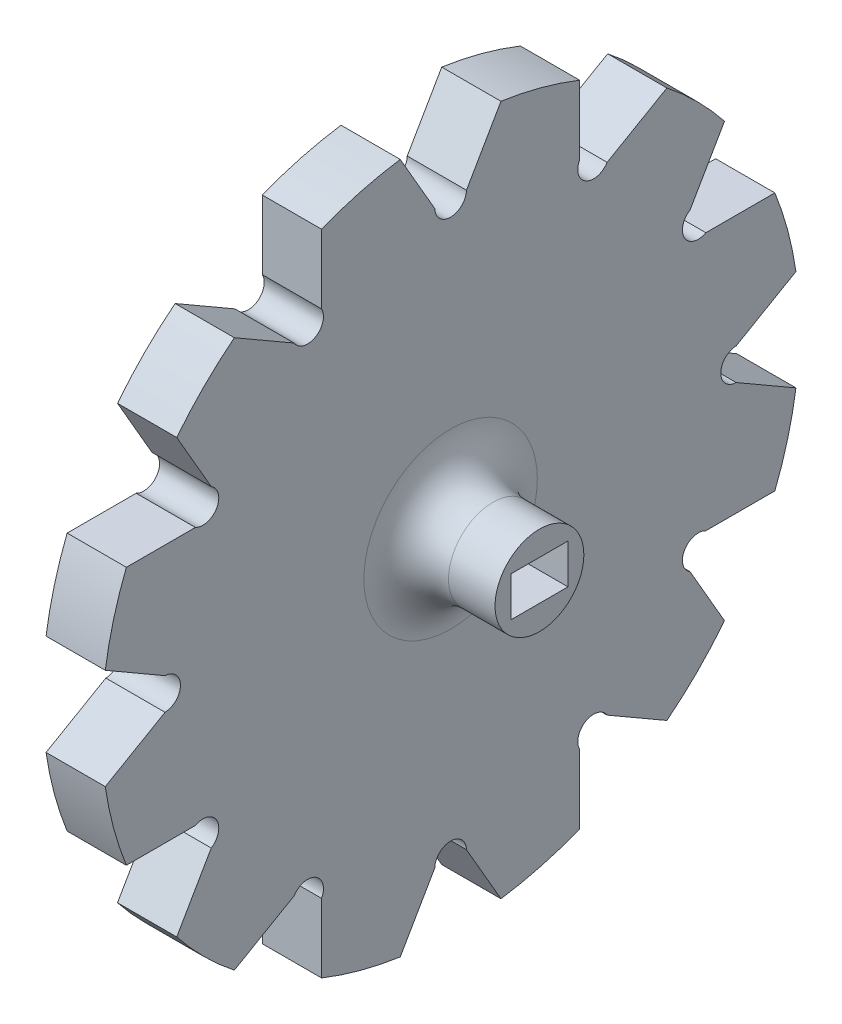
SolidWorks part; units mm, degrees
ref_plane "Front" through (0, 0, 0) normal (0, 0, 1) x (1, 0, 0)
ref_plane "Top" through (0, 0, 0) normal (0, 1, 0) x (1, 0, 0)
ref_plane "Right" through (0, 0, 0) normal (1, 0, 0) x (0, 0, -1)
sketch "Sketch3" plane through (0, 0, 0) normal (1, 0, 0) x (0, 0, -1)
  line L0 (0, -27.0459) -> (0, 27.0459) construction
  line L1 (0, 0) -> (7, 26.1244) construction
  line L2 (0, 0) -> (-7, 26.1244) construction
  circle A0 centre (0, 0) radius 27.0459
  dimension "D1" = 15
  dimension "D2" = 14
extrude "Boss-Extrude1" add sketch "Sketch3" along normal blind 5.6
sketch "Sketch4" plane through (5.6, 0, 0) normal (1, 0, 0) x (0, 0, -1)
  circle A0 centre (0, 27.0459) radius 1.5
  circle A1 centre (0, 0) radius 27.0459 construction
  circle A2 centre (13.523, 23.4225) radius 1.5
  circle A3 centre (23.4225, 13.523) radius 1.5
  circle A4 centre (27.0459, 0) radius 1.5
  circle A5 centre (23.4225, -13.523) radius 1.5
  circle A6 centre (13.523, -23.4225) radius 1.5
  circle A7 centre (0, -27.0459) radius 1.5
  circle A8 centre (-13.523, -23.4225) radius 1.5
  circle A9 centre (-23.4225, -13.523) radius 1.5
  circle A10 centre (-27.0459, 0) radius 1.5
  circle A11 centre (-23.4225, 13.523) radius 1.5
  circle A12 centre (-13.523, 23.4225) radius 1.5
  point P5 (0, 0)
  point P29 (0, 0)
  dimension "D1" = 3
  dimension "D2" = 12
extrude "Cut-Extrude1" cut sketch "Sketch4" against normal through all
sketch "Sketch5" plane through (5.6, 0, 0) normal (1, 0, 0) x (0, 0, -1)
  line L0 (0, 0) -> (8.541, 31.8756) construction
  line L1 (0, 0) -> (0, 32.6547) construction
  line L2 (1.4994, 27.0043) -> (4.7616, 32.6547)
  line L3 (12.2036, 24.1361) -> (12.2036, 30.6606)
  line L6 (1.4994, 27.0043) -> (2.6795, 10)
  line L7 (12.2036, 24.1361) -> (2.6795, 10)
  line L8 (22.6367, 14.8007) -> (7.3205, 7.3205)
  line L9 (14.8007, 22.6367) -> (7.3205, 7.3205)
  line L10 (14.8007, 22.6367) -> (20.451, 25.8989)
  line L11 (22.6367, 14.8007) -> (25.8989, 20.451)
  line L12 (27.0043, 1.4994) -> (10, 2.6795)
  line L13 (24.1361, 12.2036) -> (10, 2.6795)
  line L14 (24.1361, 12.2036) -> (30.6606, 12.2036)
  line L15 (27.0043, 1.4994) -> (32.6547, 4.7616)
  line L16 (24.1361, -12.2036) -> (10, -2.6795)
  line L17 (27.0043, -1.4994) -> (10, -2.6795)
  line L18 (27.0043, -1.4994) -> (32.6547, -4.7616)
  line L19 (24.1361, -12.2036) -> (30.6606, -12.2036)
  line L20 (14.8007, -22.6367) -> (7.3205, -7.3205)
  line L21 (22.6367, -14.8007) -> (7.3205, -7.3205)
  line L22 (22.6367, -14.8007) -> (25.8989, -20.451)
  line L23 (14.8007, -22.6367) -> (20.451, -25.8989)
  line L24 (1.4994, -27.0043) -> (2.6795, -10)
  line L25 (12.2036, -24.1361) -> (2.6795, -10)
  line L26 (12.2036, -24.1361) -> (12.2036, -30.6606)
  line L27 (1.4994, -27.0043) -> (4.7616, -32.6547)
  line L28 (-12.2036, -24.1361) -> (-2.6795, -10)
  line L29 (-1.4994, -27.0043) -> (-2.6795, -10)
  line L30 (-1.4994, -27.0043) -> (-4.7616, -32.6547)
  line L31 (-12.2036, -24.1361) -> (-12.2036, -30.6606)
  line L32 (-22.6367, -14.8007) -> (-7.3205, -7.3205)
  line L33 (-14.8007, -22.6367) -> (-7.3205, -7.3205)
  line L34 (-14.8007, -22.6367) -> (-20.451, -25.8989)
  line L35 (-22.6367, -14.8007) -> (-25.8989, -20.451)
  line L36 (-27.0043, -1.4994) -> (-10, -2.6795)
  line L37 (-24.1361, -12.2036) -> (-10, -2.6795)
  line L38 (-24.1361, -12.2036) -> (-30.6606, -12.2036)
  line L39 (-27.0043, -1.4994) -> (-32.6547, -4.7616)
  line L40 (-24.1361, 12.2036) -> (-10, 2.6795)
  line L41 (-27.0043, 1.4994) -> (-10, 2.6795)
  line L42 (-27.0043, 1.4994) -> (-32.6547, 4.7616)
  line L43 (-24.1361, 12.2036) -> (-30.6606, 12.2036)
  line L44 (-14.8007, 22.6367) -> (-7.3205, 7.3205)
  line L45 (-22.6367, 14.8007) -> (-7.3205, 7.3205)
  line L46 (-22.6367, 14.8007) -> (-25.8989, 20.451)
  line L47 (-14.8007, 22.6367) -> (-20.451, 25.8989)
  line L48 (-1.4994, 27.0043) -> (-2.6795, 10)
  line L49 (-12.2036, 24.1361) -> (-2.6795, 10)
  line L50 (-12.2036, 24.1361) -> (-12.2036, 30.6606)
  line L51 (-1.4994, 27.0043) -> (-4.7616, 32.6547)
  arc A0 (12.2036, 30.6606) -> (4.7616, 32.6547) centre (0, 0) ccw
  arc A1 (25.8989, 20.451) -> (20.451, 25.8989) centre (0, 0) ccw
  arc A2 (32.6547, 4.7616) -> (30.6606, 12.2036) centre (0, 0) ccw
  arc A3 (30.6606, -12.2036) -> (32.6547, -4.7616) centre (0, 0) ccw
  arc A4 (20.451, -25.8989) -> (25.8989, -20.451) centre (0, 0) ccw
  arc A5 (4.7616, -32.6547) -> (12.2036, -30.6606) centre (0, 0) ccw
  arc A6 (-12.2036, -30.6606) -> (-4.7616, -32.6547) centre (0, 0) ccw
  arc A7 (-25.8989, -20.451) -> (-20.451, -25.8989) centre (0, 0) ccw
  arc A8 (-32.6547, -4.7616) -> (-30.6606, -12.2036) centre (0, 0) ccw
  arc A9 (-30.6606, 12.2036) -> (-32.6547, 4.7616) centre (0, 0) ccw
  arc A10 (-20.451, 25.8989) -> (-25.8989, 20.451) centre (0, 0) ccw
  arc A11 (-4.7616, 32.6547) -> (-12.2036, 30.6606) centre (0, 0) ccw
  point P67 (0, 0)
  dimension "D1" = 66
  dimension "D2" = 15
  dimension "D3" = 30
  dimension "D4" = 10
  dimension "D5" = 12
extrude "Boss-Extrude3" add sketch "Sketch5" against normal up to surface (5.6 mm away) up to face at (0, 0, 0)
sketch "Sketch6" plane through (5.6, 0, 0) normal (1, 0, 0) x (0, 0, -1)
  circle A0 centre (0, 0) radius 4.2
  dimension "D1" = 8.4
extrude "Boss-Extrude4" add sketch "Sketch6" along normal blind 8.4
sketch "Sketch7" plane through (14, 0, 0) normal (1, 0, 0) x (0, 0, -1)
  line L1 (-2.7, 1.88) -> (2.7, 1.88)
  line L2 (-2.7, 1.88) -> (-2.7, -1.88)
  line L3 (-2.7, -1.88) -> (2.7, -1.88)
  line L4 (2.7, 1.88) -> (2.7, -1.88)
  line L5 (-2.7, 1.88) -> (2.7, -1.88) construction
  line L6 (-2.7, -1.88) -> (2.7, 1.88) construction
  point P0 (0, 0)
  dimension "D1" = 3.76
  dimension "D2" = 5.4
extrude "Cut-Extrude2" cut sketch "Sketch7" against normal blind 6
fillet "Fillet1" radius 4 1 edges at (5.6, 0, -4.2)
